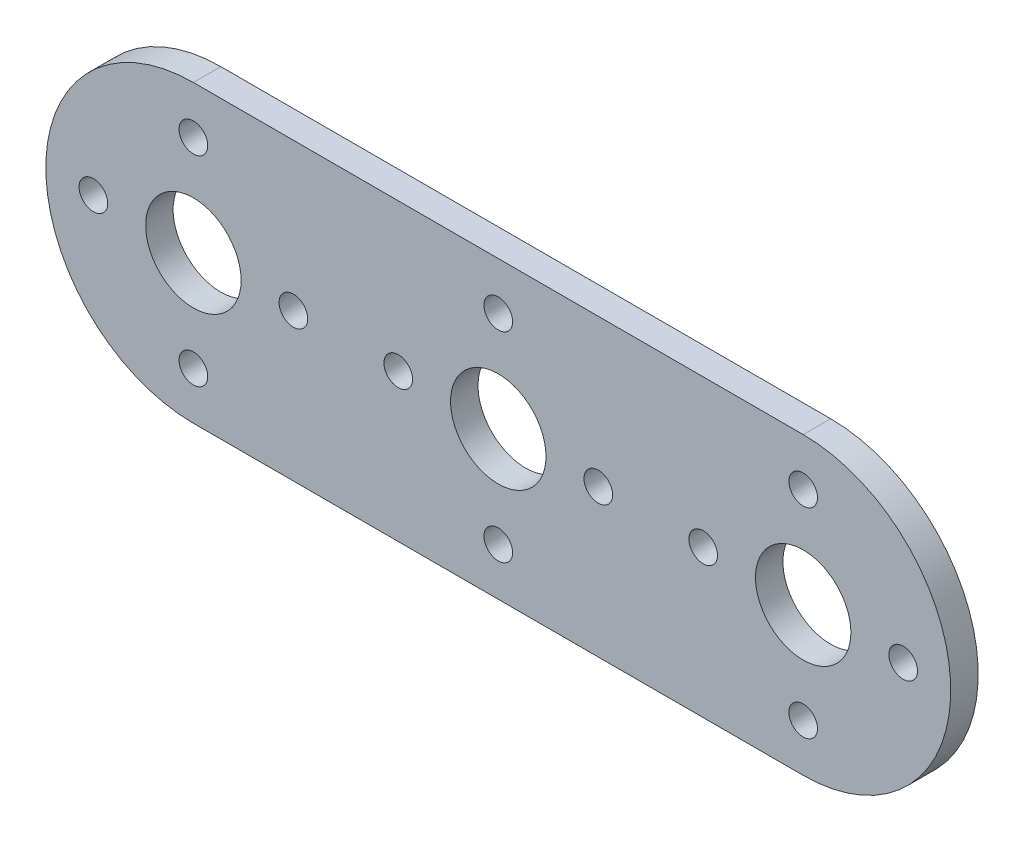
SolidWorks part; units mm, degrees
ref_plane "Front Plane" through (0, 0, 0) normal (0, 0, 1) x (1, 0, 0)
ref_plane "Top Plane" through (0, 0, 0) normal (0, 1, 0) x (1, 0, 0)
ref_plane "Right Plane" through (0, 0, 0) normal (1, 0, 0) x (0, 0, -1)
sketch "Sketch1" plane through (0, 0, 0) normal (0, 0, 1) x (1, 0, 0)
  line L0 (0, 12.2936) -> (50.8, 12.2936)
  line L1 (0, -12.2936) -> (50.8, -12.2936)
  arc A0 (0, 12.2936) -> (0, -12.2936) centre (0, 0) ccw
  arc A1 (50.8, -12.2936) -> (50.8, 12.2936) centre (50.8, 0) ccw
  circle A2 centre (0, 0) radius 3.9751
  circle A3 centre (0, 0) radius 8.3312 construction
  circle A4 centre (0, 8.3312) radius 1.1938
  circle A5 centre (8.3312, 0) radius 1.1938
  circle A6 centre (0, -8.3312) radius 1.1938
  circle A7 centre (-8.3312, 0) radius 1.1938
  circle A8 centre (17.0688, 0) radius 1.1938
  circle A9 centre (33.7312, 0) radius 1.1938
  circle A10 centre (25.4, -8.3312) radius 1.1938
  circle A11 centre (25.4, 0) radius 3.9751
  circle A12 centre (25.4, 8.3312) radius 1.1938
  circle A13 centre (42.4688, 0) radius 1.1938
  circle A14 centre (50.8, -8.3312) radius 1.1938
  circle A15 centre (59.1312, 0) radius 1.1938
  circle A16 centre (50.8, 8.3312) radius 1.1938
  circle A17 centre (50.8, 0) radius 3.9751
  dimension "D1" = 50.8
  dimension "D2" = 12.2936
  dimension "D3" = 7.9502
  dimension "D4" = 16.6624
extrude "Extrude1" add sketch "Sketch1" along normal blind 2.286
